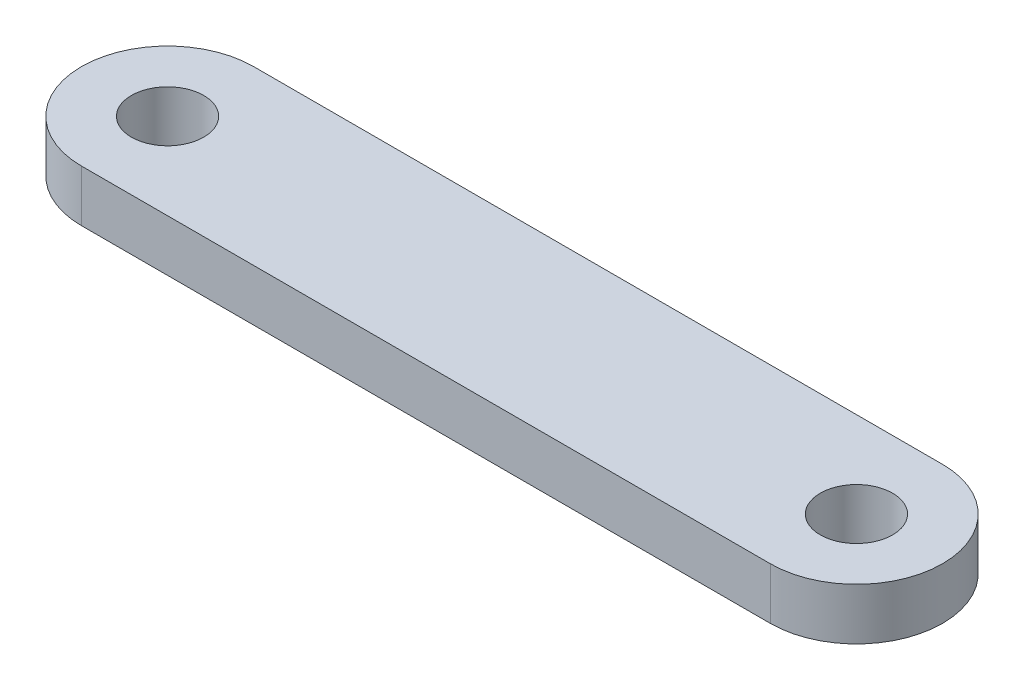
SolidWorks part; units mm, degrees
ref_plane "Front Plane" through (0, 0, 0) normal (0, 0, 1) x (1, 0, 0)
ref_plane "Top Plane" through (0, 0, 0) normal (0, 1, 0) x (1, 0, 0)
ref_plane "Right Plane" through (0, 0, 0) normal (1, 0, 0) x (0, 0, -1)
sketch "Sketch1" plane through (0, 0, 0) normal (0, 1, 0) x (1, 0, 0)
  line L1 (20, -5) -> (-20, -5)
  line L3 (20, 5) -> (-20, 5)
  line L5 (20, -5) -> (-20, 5) construction
  line L6 (20, 5) -> (-20, -5) construction
  arc A0 (-20, 5) -> (-20, -5) centre (-20, 0) ccw
  arc A1 (20, 5) -> (20, -5) centre (20, 0) cw
  point P0 (0, 0)
  point P8 (-20, 3.3402)
  dimension "D1" = 10
  dimension "D2" = 40
extrude "Boss-Extrude2" add sketch "Sketch1" along normal blind 3
sketch "Sketch3" plane through (0, 3, 0) normal (0, 1, 0) x (1, 0, 0)
  circle A0 centre (-20, 0) radius 2.1
  dimension "D1" = 4.2
extrude "Cut-Extrude3" cut sketch "Sketch3" against normal through all
mirror "Mirror1" about plane through (0, 0, 0) normal (1, 0, 0) of "Cut-Extrude3"
